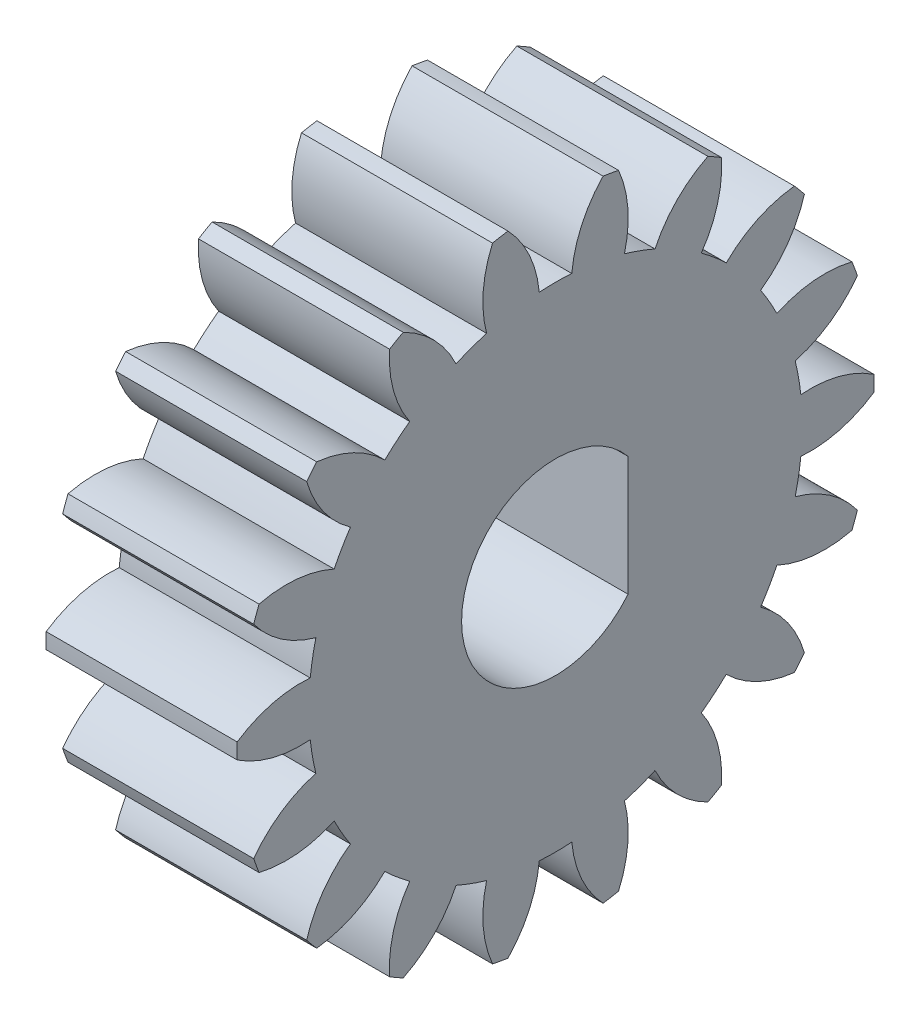
SolidWorks part; units mm, degrees
ref_plane "Plane1" through (0, 0, 0) normal (0, 0, 1) x (1, 0, 0)
ref_plane "Plane2" through (0, 0, 0) normal (0, 1, 0) x (1, 0, 0)
ref_plane "Plane3" through (0, 0, 0) normal (1, 0, 0) x (0, 0, -1)
sketch "HoldingSke" plane through (0, 0, 0) normal (0, 1, 0) x (1, 0, 0)
  line L0 (0, 0) -> (0.9511, -0.309)
  line L1 (-15, 0) -> (100, 0) construction
  line L2 (0, 0) -> (-2.1039, 2.3779)
  line L3 (0, 0) -> (-11.863, 4.5341)
  line L4 (0, 0) -> (8.2133, 2.6687)
  line L5 (0, 0) -> (-46.8476, -17.4728)
  line L6 (0, 0) -> (-4.9738, -3.3558)
  line L7 (-2.1039, 2.3779) -> (8.6588, 51.2066)
  line L8 (-76.2, 54.61) -> (-75.2, 54.61)
  line L9 (-71.009, 38.7566) -> (-53.1078, 45.2721)
  line L10 (-76.2, 71.12) -> (104.1128, 71.12)
  line L11 (0, 0) -> (-6, 0)
  line L12 (-76.2, 101.6) -> (-76.162, 101.6)
  line L13 (24.9733, 27.94) -> (52.9518, 28.4284)
  line L14 (24.9733, 27.94) -> (24.9743, 27.94)
  line L15 (24.9733, 27.94) -> (100.4006, 29.5858)
  line L16 (-63.627, -1) -> (-12.827, -1)
  circle A0 centre (0, 0) radius 3
  circle A1 centre (0, 0) radius 7.749
  circle A2 centre (0, 0) radius 37.5
  circle A3 centre (0, 0) radius 3
  dimension "MHD" = 15.498
  dimension "Hub_dia" = 75
  dimension "Bore" = 6
  dimension "MBD" = 6
  dimension "Num_teeth" = 18
  dimension "Pitch" = 1
  dimension "Overall_len" = 50
  dimension "Show_teeth" = 18
  dimension "Thickness" = 6
  dimension "OAL" = 50.0008
  dimension "T_dim" = 1
  dimension "Ap" = 20
  dimension "H" = 19.05
  dimension "Pitch_radius" = 180.3128
  dimension "Width" = 6
  dimension "Backlash" = 0.038
  dimension "Addendum_fac" = 1
  dimension "Dedendum_fac" = 1.25
  dimension "Clearance_fac" = 0.25
  dimension "Dedendum_add" = 0.001
  dimension "Module" = 1
sketch "BasProSke" plane through (0, 0, 0) normal (0, 1, 0) x (1, 0, 0)
  line L0 (-10, 0) -> (60, 0) construction
  line L1 (0, 0) -> (0, 10)
  line L2 (0, 0) -> (6, 0)
  line L3 (6, 0) -> (6, 10)
  line L4 (6, 10) -> (0, 10)
  dimension "Thickness" = 6
  dimension "Diameter" = 20
revolve "Base-Revolve" add sketch "BasProSke" angle 360 about L0
sketch "TooCutSke" plane through (0, 0, 0) normal (1, 0, 0) x (0, 0, -1)
  line L1 (0, 0) -> (0, 107) construction
  line L2 (0, 0) -> (-0.8509, 8.9597) construction
  line L3 (0, 0) -> (-3.1157, 17.6701) construction
  line L4 (-0.8509, 8.9597) -> (-1.5579, 8.835) construction
  arc A0 (0.5106, 7.7322) -> (-0.5106, 7.7322) centre (0, 0) ccw
  arc A1 (1.5152, 9.9102) -> (-1.5152, 9.9102) centre (0, 0) ccw
  circle A2 centre (0, 0) radius 9 construction
  circle A3 centre (0, 0) radius 8.4572 construction
  arc A4 (-0.5106, 7.7322) -> (-1.5152, 9.9102) centre (-4.0952, 7.3996) ccw
  arc A5 (1.5152, 9.9102) -> (0.5106, 7.7322) centre (4.0952, 7.3996) ccw
  dimension "Root_dia" = 15.498
  dimension "Overcut_dia" = 20.0508
  dimension "Pitch_dia" = 18
  dimension "Base_dia" = 16.9145
  dimension "Flank_rad" = 3.6
  dimension "Half_ang" = 10
  dimension "Half_CT" = 0.7179
extrude "ToothCut" cut sketch "TooCutSke" along normal through all
fillet "Breaks" [suppressed] radius 0.02
fillet "RootFillets" [suppressed] radius 0.251
pattern_circular "TeethCuts" count 18 every 20 about axis through (-10, 0, 0) along (1, 0, 0) of "ToothCut", "RootFillets", "Breaks"
sketch "HubNeaOneSke" plane through (0, 0, 0) normal (-1, 0, 0) x (0, 0, 1)
  circle A0 centre (0, 0) radius 7.749
  dimension "Diameter" = 15.498
extrude "HubNearOne" [suppressed] add sketch "HubNeaOneSke" along normal blind 44.0008
sketch "HubNeaBotSke" plane through (0, 0, 0) normal (-1, 0, 0) x (0, 0, 1)
  circle A0 centre (0, 0) radius 7.749
  dimension "Diameter" = 15.498
extrude "HubNearBoth" [suppressed] add sketch "HubNeaBotSke" along normal blind 22.0004
ref_plane "FarPln" through (6, 0, 0) normal (1, 0, 0) x (0, 0, -1)
sketch "HubFarSke" plane through (6, 0, 0) normal (1, 0, 0) x (0, 0, -1)
  circle A0 centre (0, 0) radius 7.749
  dimension "Diameter" = 15.498
extrude "HubFar" [suppressed] add sketch "HubFarSke" along normal blind 22.0004
sketch "KeySke" plane through (0, 0, 0) normal (1, 0, 0) x (0, 0, -1)
  line L0 (-1, 0) -> (-1, 4)
  line L1 (-1, 4) -> (1, 4)
  line L2 (1, 4) -> (1, 0)
  line L3 (0, 0) -> (0, 34) construction
  line L4 (-1, 0) -> (1, 0)
  dimension "Offset" = 4
  dimension "Width" = 2
extrude "Keyway" [suppressed] cut sketch "KeySke" along normal mid plane 100.0016
pattern_circular "Keyway2" [suppressed] count 2 every 90 about axis through (-10, 0, 0) along (1, 0, 0)
sketch "Sketch1" plane through (6, 0, 0) normal (1, 0, 0) x (0, 0, -1)
  line L0 (2.2775, 1.875) -> (2.2775, -1.875)
  arc A0 (2.2775, 1.875) -> (2.2775, -1.875) centre (0, 0) ccw
  dimension "D1" = 5.9
  dimension "D2" = 3.75
extrude "Cut-Extrude1" cut sketch "Sketch1" against normal through all
equation "' \"Module@HoldingSke\" = 6.35"
equation "' \"Num_teeth@HoldingSke\" = 12"
equation "' \"Ap@HoldingSke\" =  20"
equation "' \"Ap@HoldingSke\" = 20"
equation "' \"Width@HoldingSke\" = 0.5 * 25.4"
equation "' \"Hub_dia@HoldingSke\"= 1 * 25.4"
equation "' \"Hub_dia@HoldingSke\" = 1 * 25.4"
equation "' \"Overall_len@HoldingSke\" = 1.0 * 25.4"
equation "' \"T_dim@HoldingSke\" = 0.1 * 25.4"
equation "' \"Width@KeySke\" = 0.25 * 25.4"
equation "' \"Show_teeth@HoldingSke\" = 13"
equation "' \"Backlash@HoldingSke\" = 0.009 * 25.4"
equation "' \"Addendum_fac@HoldingSke\" = 1.0"
equation "' \"Dedendum_fac@HoldingSke\" = 1.25"
equation "' \"Dedendum_add@HoldingSke\" = 0.00005 * 25.4"
equation "' \"Clearance_fac@HoldingSke\" = 0.25"
equation "\"Pitch@HoldingSke\" = 1 / \"Module@HoldingSke\""
equation "\"Overcut_dia@TooCutSke\" = (\"Num_teeth@HoldingSke\" + 2 * \"Addendum_fac@HoldingSke\") / \"Pitch@HoldingSke\" + 0.002 * 25.4"
equation "\"Pitch_dia@TooCutSke\" = \"Num_teeth@HoldingSke\" / \"Pitch@HoldingSke\""
equation "\"Base_dia@TooCutSke\" = \"Num_teeth@HoldingSke\" / \"Pitch@HoldingSke\" * cos((\"Ap@HoldingSke\"  * 3.14159265 / 180))"
equation "\"Root_dia@TooCutSke\" = (\"Num_teeth@HoldingSke\" + 2) / \"Pitch@HoldingSke\" - 2 * (\"Addendum_fac@HoldingSke\" + \"Dedendum_fac@HoldingSke\") / \"Pitch@HoldingSke\" - \"Dedendum_add@HoldingSke\" * 2"
equation "\"Half_ang@TooCutSke\" = 180 / \"Num_teeth@HoldingSke\""
equation "\"Half_CT@TooCutSke\" = \"Num_teeth@HoldingSke\" / \"Pitch@HoldingSke\" * sin((3.14159265 / 2 / \"Num_teeth@HoldingSke\")) / 2 - 7 * \"Backlash@HoldingSke\" / 4"
equation "\"Flank_rad@TooCutSke\" = \"Num_teeth@HoldingSke\" / \"Pitch@HoldingSke\" / 5"
equation "\"Radius@RootFillets\" = \"Clearance_fac@HoldingSke\" / \"Pitch@HoldingSke\" + \"Dedendum_add@HoldingSke\""
equation "\"Break_rad@Breaks\" = 0.02 / \"Pitch@HoldingSke\""
equation "\"Thickness@HoldingSke\" = \"Width@HoldingSke\""
equation "\"OAL@HoldingSke\" = \"Thickness@HoldingSke\""
equation "\"MHD@HoldingSke\" = (\"Num_teeth@HoldingSke\" + 2) / \"Pitch@HoldingSke\" - 2 * (\"Addendum_fac@HoldingSke\" + \"Dedendum_fac@HoldingSke\")  / \"Pitch@HoldingSke\" - \"Dedendum_add@HoldingSke\" * 2"
equation "\"MBD@HoldingSke\" = (\"Num_teeth@HoldingSke\" + 2) / \"Pitch@HoldingSke\" - 2 * (\"Addendum_fac@HoldingSke\" + \"Dedendum_fac@HoldingSke\")  / \"Pitch@HoldingSke\" - \"Dedendum_add@HoldingSke\" * 2 - 0.002 * 25.4"
equation "\"MHD@HoldingSke\" = ((sgn( \"MHD@HoldingSke\" - \"Hub_dia@HoldingSke\" )-1)*( \"MHD@HoldingSke\" - \"Hub_dia@HoldingSke\" ))/-2+ \"Hub_dia@HoldingSke\""
equation "\"MBD@HoldingSke\" = ((sgn( \"MBD@HoldingSke\" - \"Bore@HoldingSke\" )-1)*( \"MBD@HoldingSke\" - \"Bore@HoldingSke\" ))/-2+ \"Bore@HoldingSke\""
equation "\"OAL@HoldingSke\" = ((sgn( \"OAL@HoldingSke\" - \"Overall_len@HoldingSke\" )+1)*( \"OAL@HoldingSke\" - \"Overall_len@HoldingSke\" ))/2 + \"Overall_len@HoldingSke\" + 0.000002 * 25.4"
equation "\"Num_teeth@TeethCuts\" = int( \"Show_teeth@HoldingSke\" ) + 1"
equation "\"Num_teeth@TeethCuts\" = ((sgn( \"Num_teeth@TeethCuts\" - \"Num_teeth@HoldingSke\" )-1)*( \"Num_teeth@TeethCuts\" - \"Num_teeth@HoldingSke\" ))/-2+ \"Num_teeth@HoldingSke\""
equation "\"Num_teeth@TeethCuts\" = ((sgn( \"Num_teeth@TeethCuts\" - 2.0)+1)*( \"Num_teeth@TeethCuts\" - 2.0))/2 +2.0"
equation "\"Angle@TeethCuts\" = 360.0 / \"Num_teeth@HoldingSke\""
equation "\"Diameter@BasProSke\" = (\"Num_teeth@HoldingSke\" + 2 * \"Addendum_fac@HoldingSke\") / \"Pitch@HoldingSke\""
equation "\"Thickness@BasProSke\"  = \"Thickness@HoldingSke\""
equation "' \"Fillet_rad@BasProSke\" =  \"Thickness@HoldingSke\" * 0.05"
equation "' \"Fillet_rad@BasProSke\" = \"Thickness@HoldingSke\" * 0.05"
equation "\"MHD@HoldingSke\" = ((sgn( \"MHD@HoldingSke\" - \"Root_dia@TooCutSke\" )-1)*( \"MHD@HoldingSke\" - \"Root_dia@TooCutSke\" ))/-2+ \"Root_dia@TooCutSke\""
equation "\"Diameter@HubNeaOneSke\" = \"MHD@HoldingSke\""
equation "\"Length@HubNearOne\" = \"OAL@HoldingSke\" - \"Thickness@BasProSke\""
equation "\"Diameter@HubNeaBotSke\" = \"MHD@HoldingSke\""
equation "\"Length@HubNearBoth\" = ( \"OAL@HoldingSke\" - \"Thickness@BasProSke\" ) / 2.0"
equation "\"Thickness@FarPln\" = \"Thickness@BasProSke\""
equation "\"Diameter@HubFarSke\" = \"MHD@HoldingSke\""
equation "\"Length@HubFar\" = ( \"OAL@HoldingSke\" - \"Thickness@BasProSke\" ) / 2.0"
equation "\"D1@Keyway\" = \"OAL@HoldingSke\" * 2.0"
equation "\"Offset@KeySke\" = \"T_dim@HoldingSke\" + \"MBD@HoldingSke\" / 2.0"
